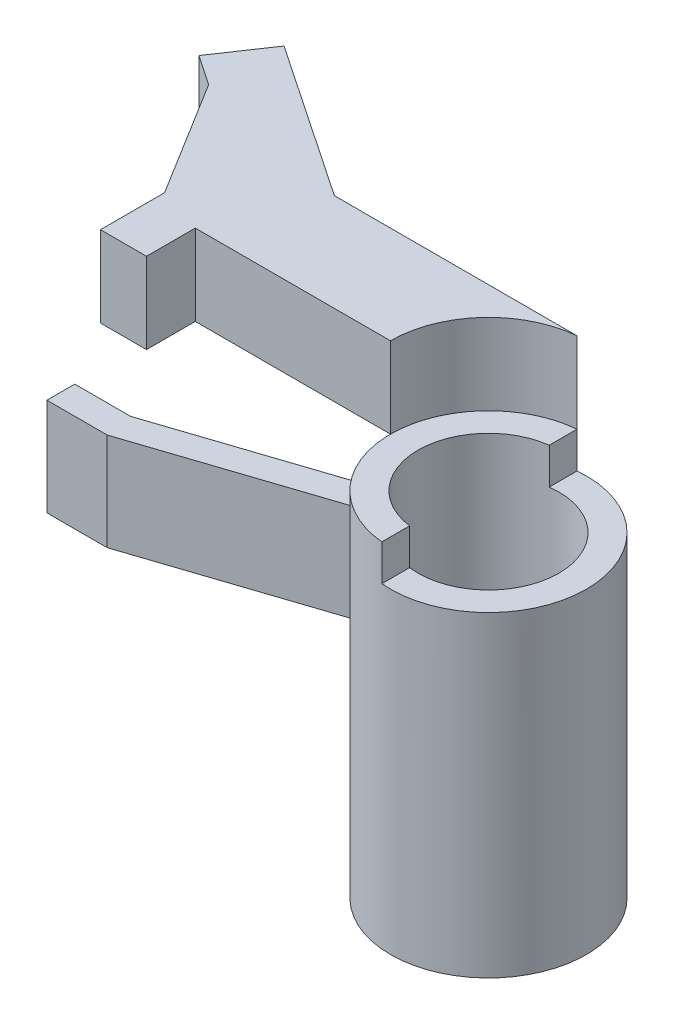
SolidWorks part; units mm, degrees
ref_plane "Front Plane" through (0, 0, 0) normal (0, 0, 1) x (1, 0, 0)
ref_plane "Top Plane" through (0, 0, 0) normal (0, 1, 0) x (1, 0, 0)
ref_plane "Right Plane" through (0, 0, 0) normal (1, 0, 0) x (0, 0, -1)
sketch "Sketch1" plane through (0, 0, 0) normal (0, 1, 0) x (1, 0, 0)
  circle A0 centre (0, 0) radius 2.525
  circle A1 centre (0, 0) radius 3.515
  dimension "D1" = 5.05
  dimension "D2" = 7.03
extrude "Boss-Extrude1" add sketch "Sketch1" along normal blind 11.35
sketch "Sketch2" plane through (0, 11.35, 0) normal (0, 1, 0) x (1, 0, 0)
  line L0 (-0.3244, 3.5) -> (-0.3244, 2.5041)
  line L1 (-0.3244, -2.5041) -> (-0.3244, -3.5)
  circle A0 centre (0, 0) radius 3.515 construction
  arc A1 (-0.3244, 3.5) -> (-0.3244, -3.5) centre (0, 0) ccw
  circle A2 centre (0, 0) radius 2.525 construction
  arc A3 (-0.3244, 2.5041) -> (-0.3244, -2.5041) centre (0, 0) ccw
  dimension "D1" = 7
extrude "Boss-Extrude2" add sketch "Sketch2" along normal blind 1.3
sketch "Sketch3" plane through (0, 12.65, 0) normal (0, 1, 0) x (1, 0, 0)
  line L0 (-0.3244, 3.5) -> (-9.0244, 3.5)
  line L1 (-9.0244, 3.5) -> (-14.5789, 7.2466)
  line L2 (-3.515, 0) -> (-10.515, 0)
  line L3 (-10.515, 0) -> (-10.515, -1.75)
  line L4 (-10.515, -1.75) -> (-12.165, -1.75)
  line L5 (-12.165, -1.75) -> (-12.165, 0.55)
  line L8 (-14.5789, 7.2466) -> (-15.8092, 5.4227)
  line L9 (-12.165, 0.55) -> (-14.7314, 4.6958)
  line L10 (-15.8092, 5.4227) -> (-14.7314, 4.6958)
  arc A0 (-0.3244, 3.5) -> (-0.3244, -3.5) centre (0, 0) ccw construction
  arc A1 (-0.3244, 3.5) -> (-3.515, 0) centre (0, 0) ccw
  dimension "D1" = 7
  dimension "D2" = 8.7
  dimension "D3" = 6.7
  dimension "D4" = 146
  dimension "D5" = 2.2
  dimension "D6" = 1.3
  dimension "D7" = 1.65
  dimension "D8" = 1.75
  dimension "D9" = 2.3
extrude "Boss-Extrude3" add sketch "Sketch3" along normal blind 2.9 separate body
sketch "Sketch5" plane through (0, 0, 0) normal (0, 1, 0) x (1, 0, 0)
  line L0 (-3.3698, -1) -> (-9.7297, -3.1074)
  line L1 (-9.7297, -3.1074) -> (-11.7297, -3.1074)
  line L2 (-11.7297, -3.1074) -> (-11.7297, -4.1059)
  line L3 (-10.515, 0) -> (-3.515, 0) construction
  line L4 (-3.0552, -1.9492) -> (-9.5683, -4.1074)
  line L5 (-9.5683, -4.1074) -> (-10.7297, -4.1074)
  line L6 (-10.7297, -4.1074) -> (-10.7297, -4.1074)
  line L7 (-10.7297, -4.1074) -> (-11.7297, -4.1059)
  line L8 (-3.0552, -1.9492) -> (-2.925, -1.9492)
  arc A0 (-0.3244, 3.5) -> (-0.3244, -3.5) centre (0, 0) ccw construction
  arc A1 (-0.3244, 3.5) -> (-0.3244, -3.5) centre (0, 0) ccw
  dimension "D1" = 1
  dimension "D2" = 6.7
  dimension "D3" = 2
  dimension "D4" = 1
ref_plane "Plane1" through (0, 11.65, 0) normal (0, 1, 0) x (1, 0, 0)
sketch "Sketch6" plane through (0, 11.65, 0) normal (0, 1, 0) x (1, 0, 0)
  line L0 (-3.3698, -1) -> (-9.7297, -3.1074)
  line L1 (-9.7297, -3.1074) -> (-11.7297, -3.1074)
  line L2 (-11.7297, -3.1074) -> (-11.7297, -4.1059)
  line L3 (-11.7297, -4.1059) -> (-9.5683, -4.1074)
  line L4 (-9.5683, -4.1074) -> (-2.9483, -1.9138)
  arc A0 (-0.3244, 3.5) -> (-0.3244, -3.5) centre (0, 0) ccw construction
  arc A1 (-3.3698, -1) -> (-2.9483, -1.9138) centre (0, 0) ccw
extrude "Boss-Extrude4" add sketch "Sketch6" against normal blind 3.5
